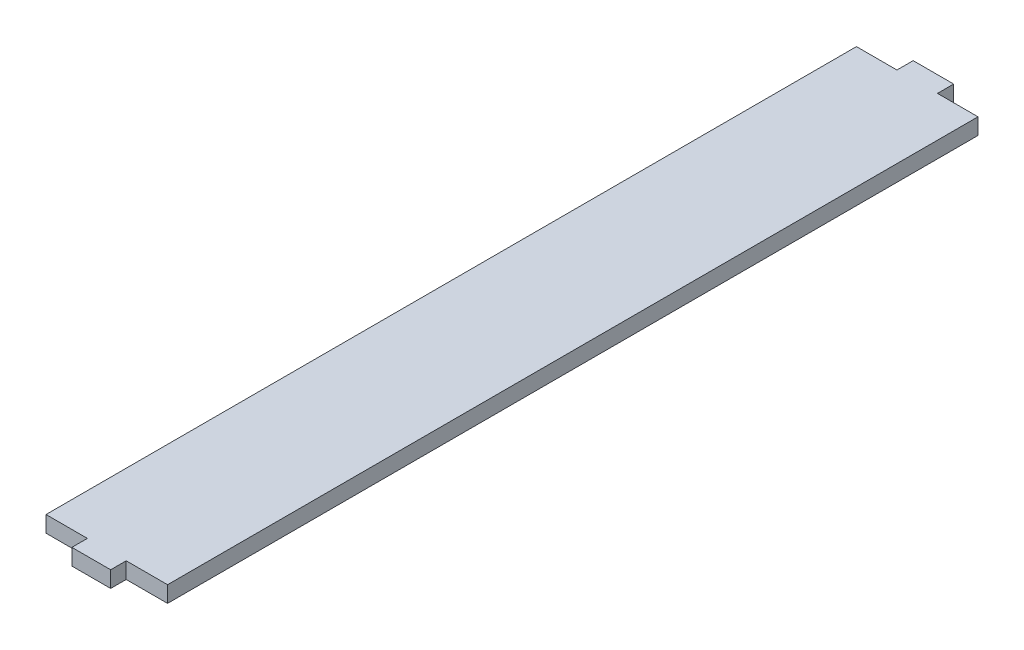
SolidWorks part; units mm, degrees
ref_plane "Front Plane" through (0, 0, 0) normal (0, 0, 1) x (1, 0, 0)
ref_plane "Top Plane" through (0, 0, 0) normal (0, 1, 0) x (1, 0, 0)
ref_plane "Right Plane" through (0, 0, 0) normal (1, 0, 0) x (0, 0, -1)
sketch "Sketch1" plane through (0, 0, 0) normal (0, 1, 0) x (1, 0, 0)
  line L0 (75.0603, -35.3928) -> (84.6361, -35.3928)
  line L1 (64.8482, 168.4375) -> (94.8482, 168.4375)
  line L2 (64.8482, 168.4375) -> (64.8482, -31.5625)
  line L3 (64.8482, -31.5625) -> (94.8482, -31.5625)
  line L4 (94.8482, 168.4375) -> (94.8482, -31.5625)
  line L5 (74.8482, 164.4375) -> (84.8482, 164.4375)
  line L6 (74.8482, 164.4375) -> (74.8482, 172.4375)
  line L7 (74.8482, 172.4375) -> (84.8482, 172.4375)
  line L8 (84.8482, 164.4375) -> (84.8482, 172.4375)
  line L9 (74.8482, 164.4375) -> (84.8482, 172.4375) construction
  line L10 (74.8482, 172.4375) -> (84.8482, 164.4375) construction
  line L11 (75.0603, -35.3928) -> (75.0603, -27.7322)
  line L12 (75.0603, -27.7322) -> (84.6361, -27.7322)
  line L13 (84.6361, -35.3928) -> (84.6361, -27.7322)
  line L14 (75.0603, -35.3928) -> (84.6361, -27.7322) construction
  line L15 (75.0603, -27.7322) -> (84.6361, -35.3928) construction
  point P4 (79.8482, 168.4375)
  point P9 (79.8482, -31.5625)
  dimension "D1" = 200
  dimension "D2" = 30
  dimension "D3" = 10
  dimension "D4" = 4
extrude "Boss-Extrude1" add sketch "Sketch1" along normal blind 4 contours L13 L3 L4 L1 L8 L5 L6 L2 L11 L12
equation "\"mat\"=\"mat@V1.assembly\""
equation "\"D4@Sketch1\"=\"mat\""
equation "\"D1@Boss-Extrude1\"=\"mat\""
